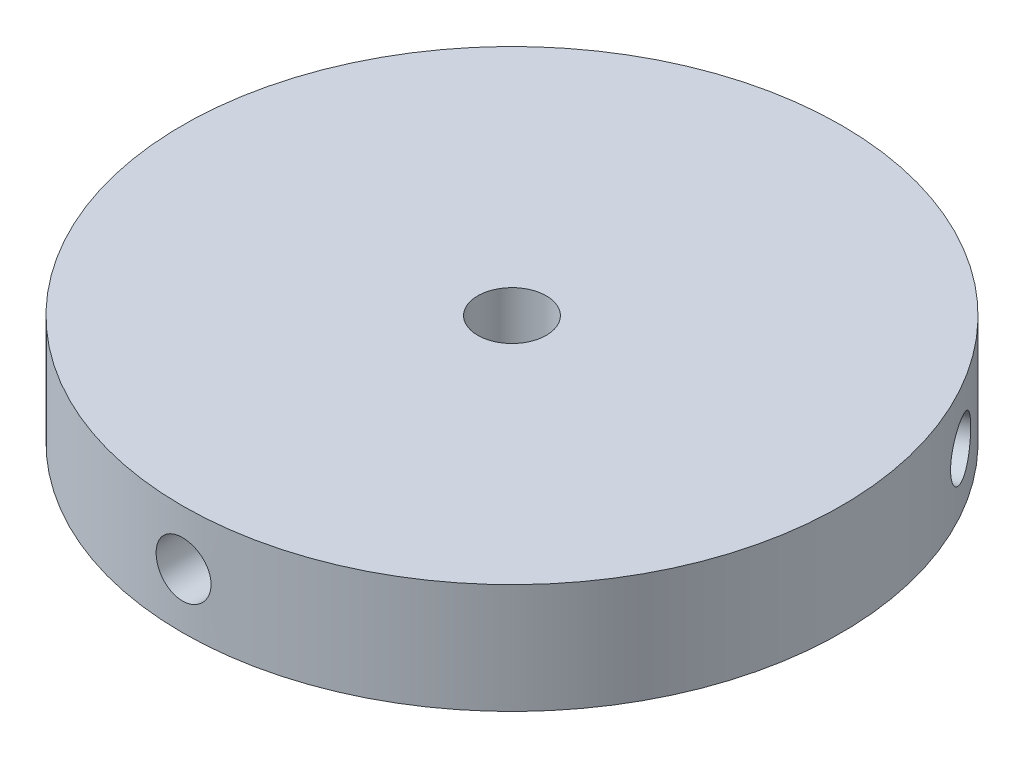
SolidWorks part; units mm, degrees
material "G10 Fiberglass"
ref_plane "Front Plane" through (0, 0, 0) normal (0, 0, 1) x (1, 0, 0)
ref_plane "Top Plane" through (0, 0, 0) normal (0, 1, 0) x (1, 0, 0)
ref_plane "Right Plane" through (0, 0, 0) normal (1, 0, 0) x (0, 0, -1)
sketch "Sketch1" plane through (0, 0, 0) normal (0, 1, 0) x (1, 0, 0)
  circle A0 centre (0, 0) radius 38.1
  dimension "D1" = 76.2
extrude "Boss-Extrude1" add sketch "Sketch1" along normal blind 12.7 contours A0
ref_plane "Plane1" through (0, 0, 38.1) normal (0, 0, 1) x (1, 0, 0)
sketch "Sketch2" plane through (0, 0, 38.1) normal (0, 0, 1) x (1, 0, 0)
  line L0 (-38.1, 0) -> (38.1, 0) construction
  circle A0 centre (0, 6.35) radius 3.175
  dimension "D2" = 6.35
  dimension "D1" = 6.35
extrude "Cut-Extrude1" cut sketch "Sketch2" against normal blind 9.525
pattern_circular "CirPattern1" count 3 over 360 about axis through (0, 0, 0) along (0, 1, 0) of "Cut-Extrude1"
sketch "Sketch3" plane through (0, 12.7, 0) normal (0, 1, 0) x (1, 0, 0)
  circle A0 centre (0, 0) radius 3.9624
  dimension "D1" = 7.9248
extrude "Cut-Extrude2" cut sketch "Sketch3" against normal up to surface (12.7 mm away) contours A0 up to face at (0, 0, 38.1)
